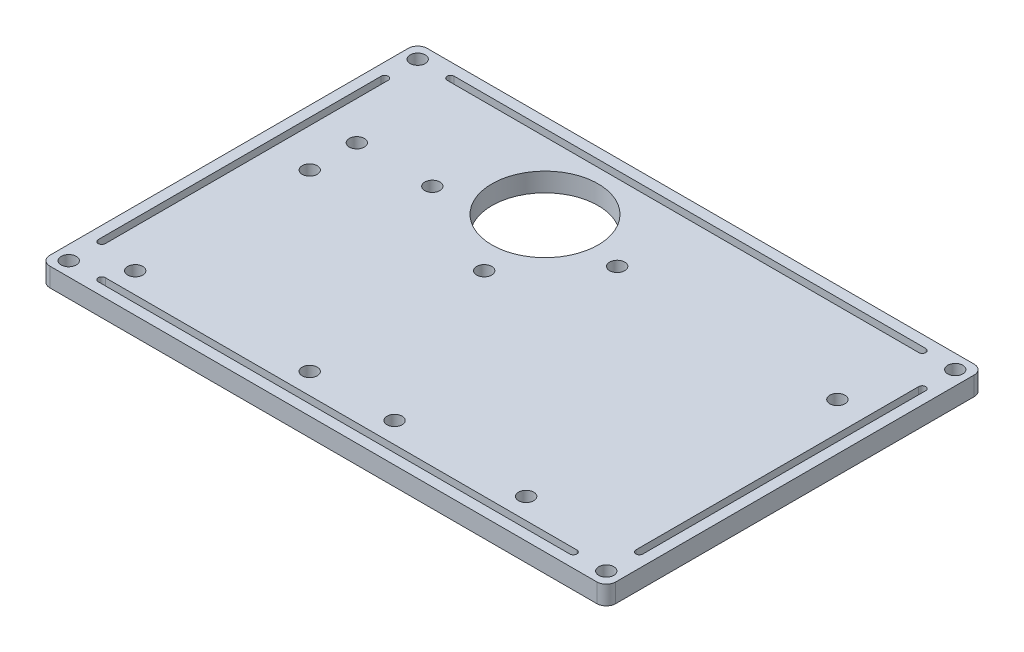
SolidWorks part; units mm, degrees
ref_plane "Front Plane" through (0, 0, 0) normal (0, 0, 1) x (1, 0, 0)
ref_plane "Top Plane" through (0, 0, 0) normal (0, 1, 0) x (1, 0, 0)
ref_plane "Right Plane" through (0, 0, 0) normal (1, 0, 0) x (0, 0, -1)
sketch "Sketch1" plane through (0, 0, 0) normal (0, 1, 0) x (1, 0, 0)
  line L0 (3, 80) -> (3, 77) construction
  line L1 (0, 0) -> (120, 0)
  line L2 (0, 0) -> (0, 80)
  line L3 (0, 80) -> (120, 80)
  line L4 (120, 0) -> (120, 80)
  line L5 (3, 77) -> (0, 77) construction
  line L6 (0, 3) -> (3, 3) construction
  line L7 (3, 3) -> (3, 0) construction
  line L8 (117, 80) -> (117, 77) construction
  line L9 (117, 77) -> (120, 77) construction
  line L10 (120, 3) -> (117, 3) construction
  line L11 (117, 3) -> (117, 0) construction
  line L12 (0, 40) -> (120, 40) construction
  line L13 (60, 80) -> (60, 0) construction
  line L14 (0, 77) -> (120, 77) construction
  line L15 (10, 77) -> (110, 77) construction
  line L16 (10, 77.75) -> (110, 77.75)
  line L19 (10, 76.25) -> (110, 76.25)
  line L20 (3, 80) -> (3, 0) construction
  line L23 (3, 70) -> (3, 10) construction
  line L24 (3.75, 70) -> (3.75, 10)
  line L25 (2.25, 70) -> (2.25, 10)
  line L28 (0, 3) -> (120, 3) construction
  line L29 (10, 3) -> (110, 3) construction
  line L32 (10, 3.75) -> (110, 3.75)
  line L33 (10, 2.25) -> (110, 2.25)
  line L34 (117, 80) -> (117, 0) construction
  line L35 (117, 70) -> (117, 10) construction
  line L36 (117.75, 70) -> (117.75, 10)
  line L37 (116.25, 70) -> (116.25, 10)
  line L38 (110, 77) -> (110, 59) construction
  line L39 (110, 59) -> (120, 59) construction
  line L41 (110, 59) -> (110, 8.2) construction
  line L42 (110, 8.2) -> (94.8, 8.2) construction
  line L43 (94.8, 8.2) -> (66.9, 8.2) construction
  line L44 (66.9, 8.2) -> (11.9, 8.2) construction
  line L45 (11.9, 8.2) -> (11.9, 45.2) construction
  line L47 (11.9, 45.2) -> (48.9, 45.2) construction
  line L49 (11.9, 45.2) -> (11.9, 55.2) construction
  line L50 (11.9, 55.2) -> (27.9, 55.2) construction
  line L51 (60, 62) -> (45, 62) construction
  line L52 (45, 62) -> (45, 80) construction
  line L53 (66.9, 8.2) -> (66.9, 60.1) construction
  line L54 (66.9, 60.1) -> (62.2, 60.1) construction
  circle A0 centre (3, 77) radius 1.6
  circle A1 centre (3, 3) radius 1.6
  circle A2 centre (117, 77) radius 1.6
  circle A3 centre (117, 3) radius 1.6
  arc A4 (10, 77.75) -> (10, 76.25) centre (10, 77) ccw
  arc A5 (110, 76.25) -> (110, 77.75) centre (110, 77) ccw
  arc A6 (3.75, 70) -> (2.25, 70) centre (3, 70) ccw
  arc A7 (2.25, 10) -> (3.75, 10) centre (3, 10) ccw
  arc A8 (10, 3.75) -> (10, 2.25) centre (10, 3) ccw
  arc A9 (110, 2.25) -> (110, 3.75) centre (110, 3) ccw
  arc A10 (117.75, 70) -> (116.25, 70) centre (117, 70) ccw
  arc A11 (116.25, 10) -> (117.75, 10) centre (117, 10) ccw
  circle A12 centre (110, 59) radius 1.6
  circle A13 centre (94.8, 8.2) radius 1.6
  circle A14 centre (66.9, 8.2) radius 1.6
  circle A15 centre (11.9, 8.2) radius 1.6
  circle A16 centre (48.9, 8.2) radius 1.6
  circle A17 centre (11.9, 45.2) radius 1.6
  circle A18 centre (48.9, 45.2) radius 1.6
  circle A19 centre (11.9, 55.2) radius 1.6
  circle A20 centre (27.9, 55.2) radius 1.6
  circle A21 centre (45, 62) radius 11.25
  circle A22 centre (62.2, 60.1) radius 1.6
  point P27 (60, 77)
  point P35 (3, 40)
  point P41 (60, 3)
  point P48 (117, 40)
  dimension "D5" = 3.2
  dimension "D8" = 3.2
  dimension "D11" = 3.2
  dimension "D14" = 3.2
  dimension "D16" = 1.5
  dimension "D17" = 1.5
  dimension "D18" = 60
  dimension "D19" = 100
  dimension "D20" = 1.5
  dimension "D21" = 60
  dimension "D22" = 1.5
  dimension "D24" = 3.2
  dimension "D27" = 3.2
  dimension "D29" = 3.2
  dimension "D31" = 3.2
  dimension "D33" = 3.2
  dimension "D35" = 3.2
  dimension "D37" = 3.2
  dimension "D40" = 3.2
  dimension "D41" = 3.2
  dimension "D44" = 22.5
  dimension "D47" = 3.2
  dimension "D1" = 80
  dimension "D2" = 120
  dimension "D3" = 3
  dimension "D4" = 3
  dimension "D6" = 3
  dimension "D7" = 3
  dimension "D9" = 3
  dimension "D10" = 3
  dimension "D12" = 3
  dimension "D13" = 3
  dimension "D15" = 100
  dimension "D23" = 18
  dimension "D25" = 50.8
  dimension "D26" = 15.2
  dimension "D28" = 27.9
  dimension "D30" = 55
  dimension "D32" = 37
  dimension "D34" = 37
  dimension "D36" = 37
  dimension "D38" = 10
  dimension "D39" = 16
  dimension "D42" = 15
  dimension "D43" = 18
  dimension "D45" = 51.9
  dimension "D46" = 4.7
extrude "Boss-Extrude3" add sketch "Sketch1" along normal blind 4
fillet "Fillet5" radius 2 1 edges at (0, 2, 0)
fillet "Fillet6" radius 2 1 edges at (0, 2, -80)
fillet "Fillet7" radius 2 1 edges at (120, 2, -80)
fillet "Fillet8" radius 2 1 edges at (120, 2, 0)
